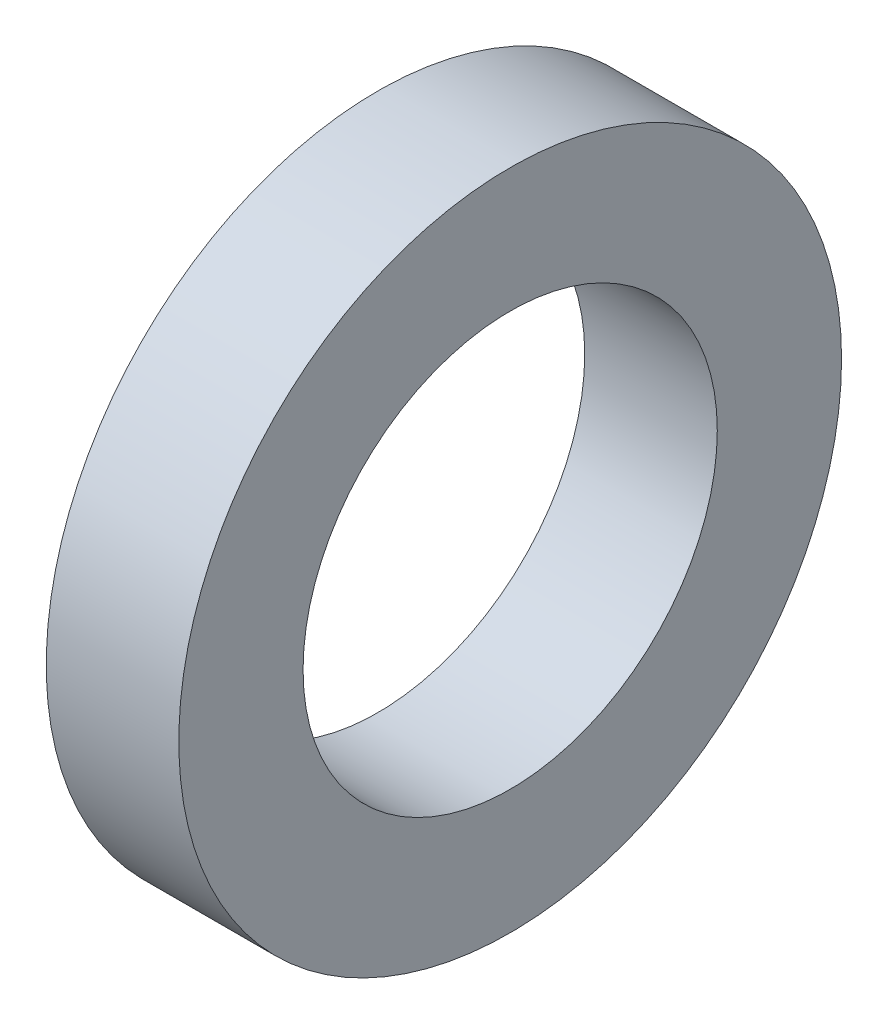
SolidWorks part; units mm, degrees
material "AISI 1035 Steel (SS)"
ref_plane "Front Plane" through (0, 0, 0) normal (0, 0, 1) x (1, 0, 0)
ref_plane "Top Plane" through (0, 0, 0) normal (0, 1, 0) x (1, 0, 0)
ref_plane "Right Plane" through (0, 0, 0) normal (1, 0, 0) x (0, 0, -1)
sketch "Sketch1" plane through (0, 0, 0) normal (1, 0, 0) x (0, 0, -1)
  circle A0 centre (0, 0) radius 12.7
  dimension "D1" = 25.4
extrude "Boss-Extrude1" add sketch "Sketch1" along normal blind 5.08
sketch "Sketch2" plane through (5.08, 0, 0) normal (1, 0, 0) x (0, 0, -1)
  point P0 (0, 0)
hole_wizard "#97 (0.625) Diameter Hole1" positions "Sketch2" profile "Sketch3" hole size "#97" standard "ANSI Inch" end condition through all
sketch "Sketch3" plane through (5.08, 0, 0) normal (0, 1, 0) x (0, 0, -1)
  line L0 (0, 0) -> (0, 5.08)
  line L1 (0, 5.08) -> (7.9375, 5.08)
  line L2 (7.9375, 5.08) -> (7.9375, 0)
  line L5 (7.9375, 0) -> (0, 0)
  line L11 (0, -6.35) -> (0, 107.95) construction
  dimension "Thru Hole Dia." = 15.875
  dimension "Thru Hole Depth" = 5.08
